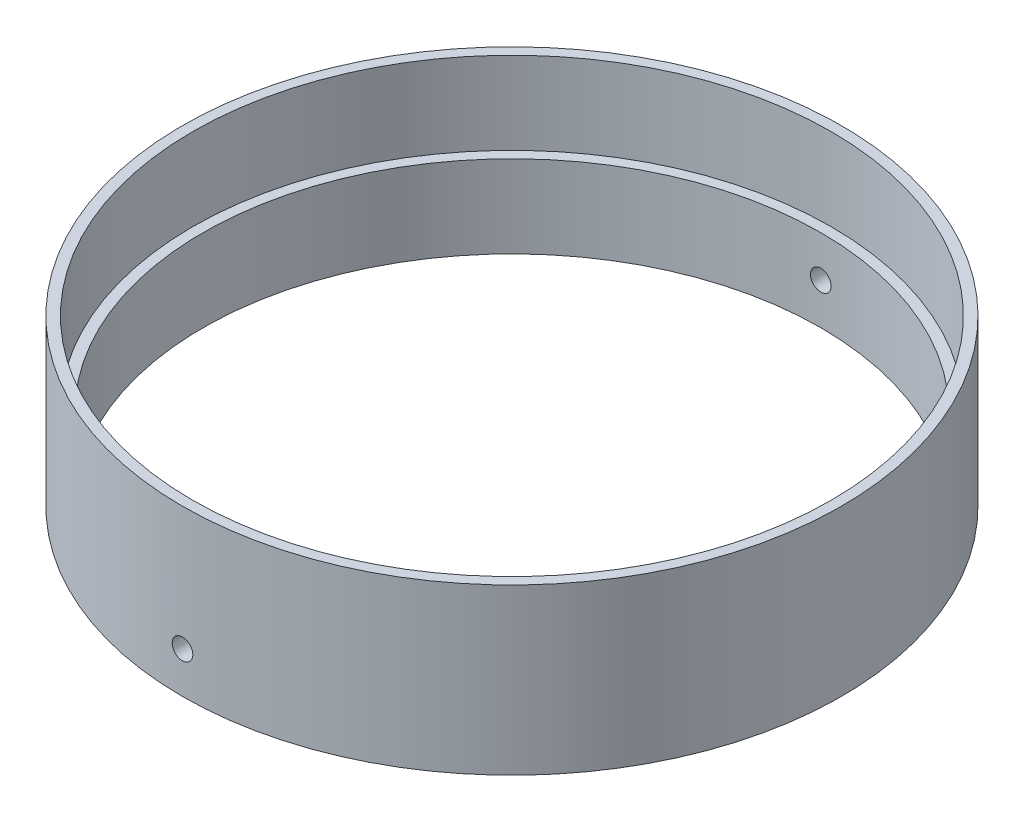
SolidWorks part; units mm, degrees
ref_plane "Front Plane" through (0, 0, 0) normal (0, 0, 1) x (1, 0, 0)
ref_plane "Top Plane" through (0, 0, 0) normal (0, 1, 0) x (1, 0, 0)
ref_plane "Right Plane" through (0, 0, 0) normal (1, 0, 0) x (0, 0, -1)
sketch "Sketch1" plane through (0, 0, 0) normal (0, 1, 0) x (1, 0, 0)
  circle A0 centre (0, 0) radius 101.6
  circle A1 centre (0, 0) radius 95.25
  dimension "D1" = 203.2
  dimension "D2" = 190.5
extrude "Boss-Extrude1" add sketch "Sketch1" along normal blind 25.4
sketch "Sketch2" plane through (0, 0, 0) normal (0, 0, 1) x (1, 0, 0)
  circle A0 centre (0, 12.7) radius 3.175
  dimension "D1" = 6.35
extrude "Cut-Extrude1" cut sketch "Sketch2" against normal through all and the other way through all
sketch "Sketch3" plane through (0, 0, 0) normal (1, 0, 0) x (0, 0, -1)
  circle A0 centre (0, 12.7) radius 1.5875
  dimension "D1" = 3.175
extrude "Cut-Extrude3" [suppressed] cut sketch "Sketch3" against normal through all
sketch "Sketch4" plane through (0, 0, 0) normal (1, 0, 0) x (0, 0, -1)
  line L0 (0, 0) -> (0, 72.5565) construction
pattern_circular "CirPattern1" [suppressed] count 24 over 360 about axis through (0, 0, 0) along (0, 1, 0)
sketch "Sketch5" plane through (0, 25.4, 0) normal (0, 1, 0) x (1, 0, 0)
  circle A0 centre (0, 0) radius 98.425
  circle A1 centre (0, 0) radius 101.6
extrude "Boss-Extrude2" add sketch "Sketch5" along normal blind 146.05
sketch "Sketch6" plane through (0, 0, 0) normal (0, -1, 0) x (1, 0, 0)
  circle A0 centre (0, 0) radius 101.6
  circle A1 centre (0, 0) radius 98.425
extrude "Boss-Extrude3" [suppressed] add sketch "Sketch6" along normal blind 133.35
ref_plane "Plane1" through (0, 0, 101.6) normal (0, 0, 1) x (1, 0, 0)
sketch "Sketch9" plane through (0, 0, 101.6) normal (0, 0, 1) x (1, 0, 0)
  line L0 (-101.6, 0) -> (101.6, 0) construction
  line L1 (0, 0) -> (0, 72.5565) construction
  circle A0 centre (-85.075, 156.8) radius 2.1
  dimension "D1" = 156.8
  dimension "D2" = 85.075
extrude "Cut-Extrude5" cut sketch "Sketch9" against normal through all
sketch "Sketch10" plane through (0, 171.45, 0) normal (0, 1, 0) x (1, 0, 0)
  circle A0 centre (0, 0) radius 101.6
extrude "Cut-Extrude6" cut sketch "Sketch10" against normal blind 120.65
